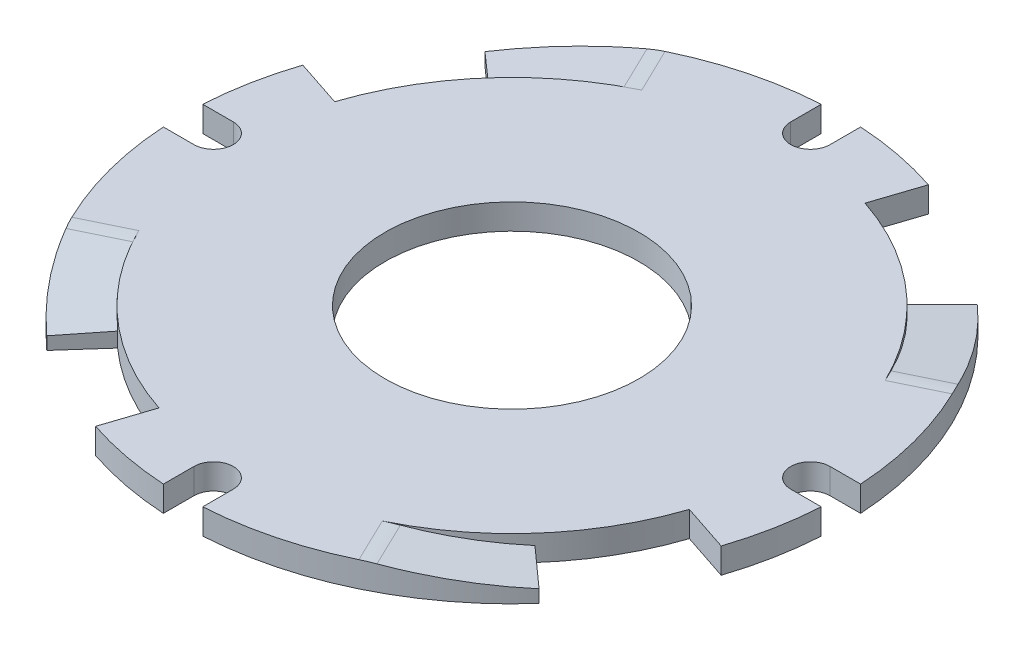
SolidWorks part; units mm, degrees
ref_plane "Plan de face" through (0, 0, 0) normal (0, 0, 1) x (1, 0, 0)
ref_plane "Plan de dessus" through (0, 0, 0) normal (0, 1, 0) x (1, 0, 0)
ref_plane "Plan de droite" through (0, 0, 0) normal (1, 0, 0) x (0, 0, -1)
sketch "Esquisse2" plane through (0, 0, 0) normal (0, 1, 0) x (1, 0, 0)
  line L0 (0, 28.4711) -> (0, 25.1) construction
  line L1 (-32.7175, 0) -> (33.1219, 0) construction
  line L2 (-1.55, 25.9037) -> (-1.55, 23.5)
  line L3 (1.55, 25.9037) -> (1.55, 23.5)
  line L4 (0, 22) -> (0, -30.0888) construction
  line L5 (19.3836, -17.2533) -> (16.4331, -14.6271)
  line L6 (24.6336, -8.1601) -> (20.884, -6.918)
  line L7 (25.9037, -1.55) -> (23.5, -1.55)
  line L8 (25.9037, 1.55) -> (23.5, 1.55)
  line L9 (-17.2533, -19.3836) -> (-14.6271, -16.4331)
  line L10 (-8.1601, -24.6336) -> (-6.918, -20.884)
  line L11 (0, 0) -> (28.0458, 48.5767) construction
  line L12 (8.1601, 24.6336) -> (6.918, 20.884)
  line L13 (17.2533, 19.3836) -> (14.6271, 16.4331)
  line L14 (-1.55, -25.9037) -> (-1.55, -23.5)
  line L15 (1.55, -25.9037) -> (1.55, -23.5)
  line L16 (-19.3836, 17.2533) -> (-16.4331, 14.6271)
  line L17 (-24.6336, 8.1601) -> (-20.884, 6.918)
  line L18 (-25.9037, 1.55) -> (-23.5, 1.55)
  line L19 (-25.9037, -1.55) -> (-23.5, -1.55)
  line L20 (0, 0) -> (23.3578, 11.3056) construction
  arc A1 (-1.55, 23.5) -> (1.55, 23.5) centre (0, 23.5) ccw
  arc A4 (1.55, 25.9037) -> (8.1601, 24.6336) centre (0, 0) cw
  arc A5 (16.4331, -14.6271) -> (20.884, -6.918) centre (0, 0) ccw
  arc A6 (14.6271, 16.4331) -> (6.918, 20.884) centre (0, 0) ccw
  arc A7 (25.9037, -1.55) -> (24.6336, -8.1601) centre (0, 0) cw
  arc A8 (23.5, 1.55) -> (23.5, -1.55) centre (23.5, 0) ccw
  arc A9 (-14.6271, -16.4331) -> (-6.918, -20.884) centre (0, 0) ccw
  arc A10 (-1.55, -25.9037) -> (-8.1601, -24.6336) centre (0, 0) cw
  arc A11 (1.55, -23.5) -> (-1.55, -23.5) centre (0, -23.5) ccw
  arc A12 (-16.4331, 14.6271) -> (-20.884, 6.918) centre (0, 0) ccw
  arc A13 (-25.9037, 1.55) -> (-24.6336, 8.1601) centre (0, 0) cw
  arc A14 (-23.5, -1.55) -> (-23.5, 1.55) centre (-23.5, 0) ccw
  arc A15 (-1.55, 25.9037) -> (-19.3836, 17.2533) centre (0, 0) ccw
  arc A16 (-25.9037, -1.55) -> (-17.2533, -19.3836) centre (0, 0) ccw
  arc A17 (1.55, -25.9037) -> (19.3836, -17.2533) centre (0, 0) ccw
  arc A18 (25.9037, 1.55) -> (17.2533, 19.3836) centre (0, 0) ccw
  circle A19 centre (0, 0) radius 10
  point P34 (0, 0)
  point P50 (0, 0)
  point P51 (0, 0)
  dimension "D1" = 3.1
  dimension "D2" = 25.95
  dimension "D5" = 22
  dimension "D9" = 20
  dimension "D3" = 30
  dimension "D4" = 5.25
  dimension "D6" = 23.5
  dimension "D8" = 22.5
  dimension "D7" = 4
extrude "Boss.-Extru.1" add sketch "Esquisse2" along normal blind 2
ref_plane "Plan1" through (23.3578, 0, -11.3056) normal (0.9001, 0, -0.4357) x (-0.4357, 0, -0.9001)
sketch "Esquisse4" plane through (23.3578, 0, -11.3056) normal (0.9001, 0, -0.4357) x (-0.4357, 0, -0.9001)
  line L1 (9.9306, 1) -> (9.9306, 3)
  line L2 (0, 3) -> (9.9306, 3)
  line L3 (0, 3) -> (0, 2)
  line L4 (9.9306, 2) -> (-9.8902, 2) construction
  line L5 (9.9306, 2) -> (9.9306, 0) construction
  line L6 (1.0578, 1.9439) -> (9.9306, 1)
  arc A0 (0, 2) -> (1.0578, 1.9439) centre (0, -8) cw
  point P2 (0, 0)
  point P5 (0, 0)
  point P9 (0, 5.0743)
  dimension "D2" = 10
  dimension "D1" = 1
  dimension "D3" = 1
extrude "Enlèv. mat.-Extru.1" cut sketch "Esquisse4" against normal up to surface (3.95 mm away)
pattern_circular "Répétition circulaire1" count 4 over 360 about axis through (0, 0, 0) along (0, 1, 0) of "Enlèv. mat.-Extru.1"
